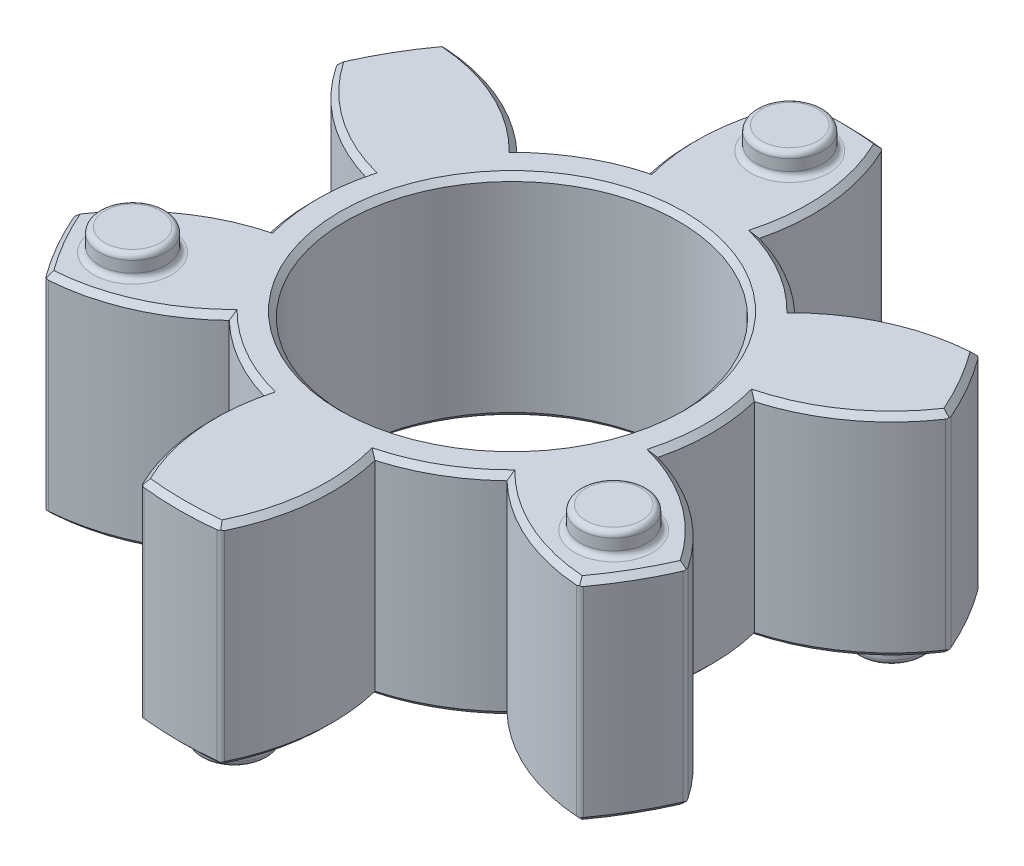
SolidWorks part; units mm, degrees
material "Polyurethane Foam Rigid"
ref_plane "Front Plane" through (0, 0, 0) normal (0, 0, 1) x (1, 0, 0)
ref_plane "Top Plane" through (0, 0, 0) normal (0, 1, 0) x (1, 0, 0)
ref_plane "Right Plane" through (0, 0, 0) normal (1, 0, 0) x (0, 0, -1)
sketch "Body Sketch" plane through (0, 0, 0) normal (0, 1, 0) x (1, 0, 0)
  circle A0 centre (0, 0) radius 15
  dimension "D" = 30
extrude "Body" add sketch "Body Sketch" along normal mid plane 9.5
sketch "Body Hole Sketch" plane through (0, 0, 0) normal (0, 1, 0) x (1, 0, 0)
  circle A0 centre (0, 0) radius 7.5
  dimension "d1" = 15
extrude "Body Hole" cut sketch "Body Hole Sketch" along normal through all both and the other way through all
sketch "Leg Skech" plane through (0, 0, 0) normal (0, 1, 0) x (1, 0, 0)
  arc A0 (-2.4833, 8.6506) -> (-6.25, 6.4759) centre (0, 0) ccw
  arc A1 (14.9833, 8.6506) -> (6.25, 6.4759) centre (12.5, 0) ccw
  arc A2 (14.9833, -8.6506) -> (8.7333, -2.1747) centre (6.25, -10.8253) ccw
  arc A3 (0, -17.3012) -> (2.4833, -8.6506) centre (-6.25, -10.8253) ccw
  arc A4 (-14.9833, -8.6506) -> (-6.25, -6.4759) centre (-12.5, 0) ccw
  arc A5 (-14.9833, 8.6506) -> (-8.7333, 2.1747) centre (-6.25, 10.8253) ccw
  arc A6 (0, 17.3012) -> (-2.4833, 8.6506) centre (6.25, 10.8253) ccw
  arc A7 (2.4833, 8.6506) -> (0, 17.3012) centre (-6.25, 10.8253) ccw
  arc A8 (8.7333, 2.1747) -> (14.9833, 8.6506) centre (6.25, 10.8253) ccw
  arc A9 (6.25, -6.4759) -> (14.9833, -8.6506) centre (12.5, 0) ccw
  arc A10 (-2.4833, -8.6506) -> (0, -17.3012) centre (6.25, -10.8253) ccw
  arc A11 (-6.25, 6.4759) -> (-14.9833, 8.6506) centre (-12.5, 0) ccw
  arc A12 (-8.7333, -2.1747) -> (-14.9833, -8.6506) centre (-6.25, -10.8253) ccw
  arc A13 (-8.7333, 2.1747) -> (-8.7333, -2.1747) centre (0, 0) ccw
  arc A14 (-6.25, -6.4759) -> (-2.4833, -8.6506) centre (0, 0) ccw
  arc A15 (2.4833, -8.6506) -> (6.25, -6.4759) centre (0, 0) ccw
  arc A16 (8.7333, -2.1747) -> (8.7333, 2.1747) centre (0, 0) ccw
  arc A17 (6.25, 6.4759) -> (2.4833, 8.6506) centre (0, 0) ccw
  point P17 (0, 0)
  dimension "D1" = 18
  dimension "D3" = 12.5
  dimension "D4" = 12.5
  dimension "D2" = 6
extrude "Legs" cut sketch "Leg Skech" along normal through all both and the other way through all flip side to cut
chamfer "Aesthetic Chamfer" distance 0.25 angle 45 50 edges at (0, 4.75, 15) (-2.6931, 4.75, 11.836) (-4.5, 4.75, 7.7942) (-8.9038, 4.75, 8.2503) (-12.9904, 4.75, 7.5) (-11.5968, 4.75, 3.5858) (-9, 4.75, 0) (-11.5968, 4.75, -3.5858) (-12.9904, 4.75, -7.5) (-8.9038, 4.75, -8.2503) (-4.5, 4.75, -7.7942) (-2.6931, 4.75, -11.836) (0, 4.75, -15) (2.6931, 4.75, -11.836) (4.5, 4.75, -7.7942) (8.9038, 4.75, -8.2503) (12.9904, 4.75, -7.5) (11.5968, 4.75, -3.5858) (9, 4.75, 0) (11.5968, 4.75, 3.5858) (12.9904, 4.75, 7.5) (8.9038, 4.75, 8.2503) (4.5, 4.75, 7.7942) (2.6931, 4.75, 11.836) (0, 4.75, 7.5) (8.9038, -4.75, 8.2503) (12.9904, -4.75, 7.5) (11.5968, -4.75, 3.5858) (9, -4.75, 0) (11.5968, -4.75, -3.5858) (12.9904, -4.75, -7.5) (8.9038, -4.75, -8.2503) (4.5, -4.75, -7.7942) (2.6931, -4.75, -11.836) (0, -4.75, -15) (-2.6931, -4.75, -11.836) (-4.5, -4.75, -7.7942) (-8.9038, -4.75, -8.2503) (-12.9904, -4.75, -7.5) (-11.5968, -4.75, -3.5858) (-9, -4.75, 0) (-11.5968, -4.75, 3.5858) (-12.9904, -4.75, 7.5) (-8.9038, -4.75, 8.2503) (-4.5, -4.75, 7.7942) (-2.6931, -4.75, 11.836) (0, -4.75, 15) (2.6931, -4.75, 11.836) (4.5, -4.75, 7.7942) (0, -4.75, 7.5)
sketch "Top Distance Sketch" plane through (0, 0, 0) normal (0, 1, 0) x (1, 0, 0)
  circle A0 centre (0, 12.5) radius 1.5
  circle A1 centre (10.8253, -6.25) radius 1.5
  circle A2 centre (-10.8253, -6.25) radius 1.5
  point P10 (0, 0)
  dimension "D1" = 3
  dimension "D2" = 12.5
  dimension "D3" = 3
extrude "Top Distance" add sketch "Top Distance Sketch" along normal blind 1 from surface at 4.75 starting at face at (0, 4.75, 0)
sketch "Bottom Distance Sketch" plane through (0, 0, 0) normal (0, 1, 0) x (1, 0, 0)
  circle A0 centre (0, -12.5) radius 1.5
  circle A1 centre (-10.8253, 6.25) radius 1.5
  circle A2 centre (10.8253, 6.25) radius 1.5
  point P9 (0, 0)
  dimension "D1" = 3
  dimension "D2" = 12.5
  dimension "D3" = 3
extrude "Bottom Distance" add sketch "Bottom Distance Sketch" against normal blind 1 from surface at -4.75 starting at face at (0, -4.75, 0)
fillet "Aesthetic Fillet" radius 0.25 24 edges at (12.01, 0, 8.9867) (13.7877, 0, 5.9076) (13.7877, 0, -5.9076) (12.01, 0, -8.9867) (1.7777, 0, -14.8943) (-1.7777, 0, -14.8943) (-12.01, 0, -8.9867) (-13.7877, 0, -5.9076) (-13.7877, 0, 5.9076) (-12.01, 0, 8.9867) (-1.7777, 0, 14.8943) (1.7777, 0, 14.8943) (0, 4.75, -11) (0, 5.75, -11) (10.8253, 4.75, 7.75) (10.8253, 5.75, 7.75) (-10.8253, 4.75, 7.75) (-10.8253, 5.75, 7.75) (-10.8253, -4.75, -4.75) (-10.8253, -5.75, -4.75) (10.8253, -4.75, -4.75) (10.8253, -5.75, -4.75) (0, -4.75, 14) (0, -5.75, 14)
equation "\"L\"= 35.00"
equation "\"L2@Body\"= ( 2 * ( \"L\" - 0.5 ) / 6 ) - 2'Body Length"
equation "\"d1@Body Hole Sketch\"= \"D@Body Sketch\" / 2'Body Hole Diameter"
equation "\"D1@Leg Skech\"= \"D@Body Sketch\" * 0.6"
equation "\"D3@Leg Skech\"= 0.5 + \"D@Body Sketch\" * 0.4'Jaw Radius"
equation "\"D4@Leg Skech\" = 0.5 + \"D@Body Sketch\" * 0.4'Jaw Radius"
equation "\"D1@Top Distance Sketch\"= \"D@Body Sketch\" / 10'Distance Radius"
equation "\"D2@Top Distance Sketch\"= 0.5 + \"D@Body Sketch\" * 0.4'Distance Position"
equation "\"D1@Bottom Distance Sketch\"= \"D@Body Sketch\" / 10'Distance Radius"
equation "\"D2@Bottom Distance Sketch\"= 0.5 + \"D@Body Sketch\" * 0.4'Distance Position"
equation "\"D3@Top Distance Sketch\"= \"D2@Leg Skech\" / 2'Number of Top Distances"
equation "\"D3@Bottom Distance Sketch\"= \"D2@Leg Skech\" / 2'Number of Bottom Distances"
